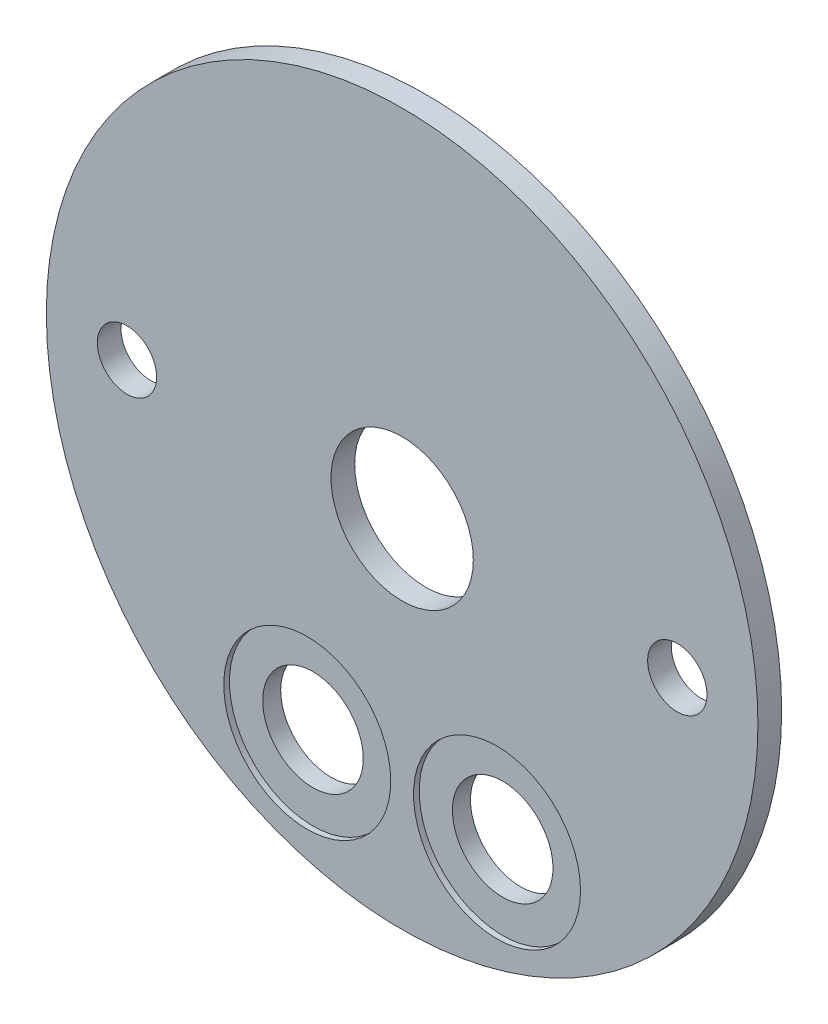
SolidWorks part; units mm, degrees
ref_plane "Front Plane" through (0, 0, 0) normal (0, 0, 1) x (1, 0, 0)
ref_plane "Top Plane" through (0, 0, 0) normal (0, 1, 0) x (1, 0, 0)
ref_plane "Right Plane" through (0, 0, 0) normal (1, 0, 0) x (0, 0, -1)
sketch "Sketch1" plane through (0, 0, 0) normal (0, 0, 1) x (1, 0, 0)
  circle A0 centre (0, 0) radius 49.5046
  dimension "D1" = 99.0092
extrude "Boss-Extrude1" add sketch "Sketch1" along normal blind 5.08
sketch "Sketch2" plane through (0, 0, 5.08) normal (0, 0, 1) x (1, 0, 0)
  circle A0 centre (0, 0) radius 47.625
  dimension "D1" = 95.25
extrude "Boss-Extrude2" add sketch "Sketch2" along normal blind 3.175
sketch "Sketch3" plane through (0, 0, 8.255) normal (0, 0, 1) x (1, 0, 0)
  circle A0 centre (-12.7, -31.1668) radius 6.731
  circle A1 centre (12.7, -31.1668) radius 6.731
  circle A2 centre (-12.7, -31.1668) radius 12.7 construction
  circle A3 centre (-12.7, -31.1668) radius 13.97 construction
  circle A4 centre (12.7, -31.1668) radius 12.7 construction
  circle A5 centre (12.7, -31.1668) radius 13.97 construction
  circle A6 centre (0, 0) radius 47.625 construction
  circle A7 centre (0, 0) radius 47.625 construction
  circle A8 centre (-36.83, 0) radius 3.9688
  circle A9 centre (36.83, 0) radius 3.9687
  circle A10 centre (0, 0) radius 9.525
  dimension "D1" = 27.94
  dimension "D2" = 25.4
  dimension "D3" = 13.462
  dimension "D4" = 7.9375
  dimension "D5" = 7.9375
  dimension "D8" = 19.05
  dimension "D6" = 73.66
  dimension "D7" = 36.83
extrude "Cut-Extrude1" cut sketch "Sketch3" against normal through all
sketch "Sketch7" plane through (0, 0, 0) normal (0, 0, -1) x (-1, 0, 0)
  circle A0 centre (0, 0) radius 65.4214
extrude "Cut-Extrude3" cut sketch "Sketch7" against normal blind 5.08
sketch "Sketch9" plane through (0, 0, 8.255) normal (0, 0, 1) x (1, 0, 0)
  circle A0 centre (-12.7, -31.1668) radius 11.176
  circle A1 centre (12.7, -31.1668) radius 11.176
  dimension "D1" = 22.352
  dimension "D2" = 22.352
extrude "Cut-Extrude5" cut sketch "Sketch9" against normal blind 0.762
